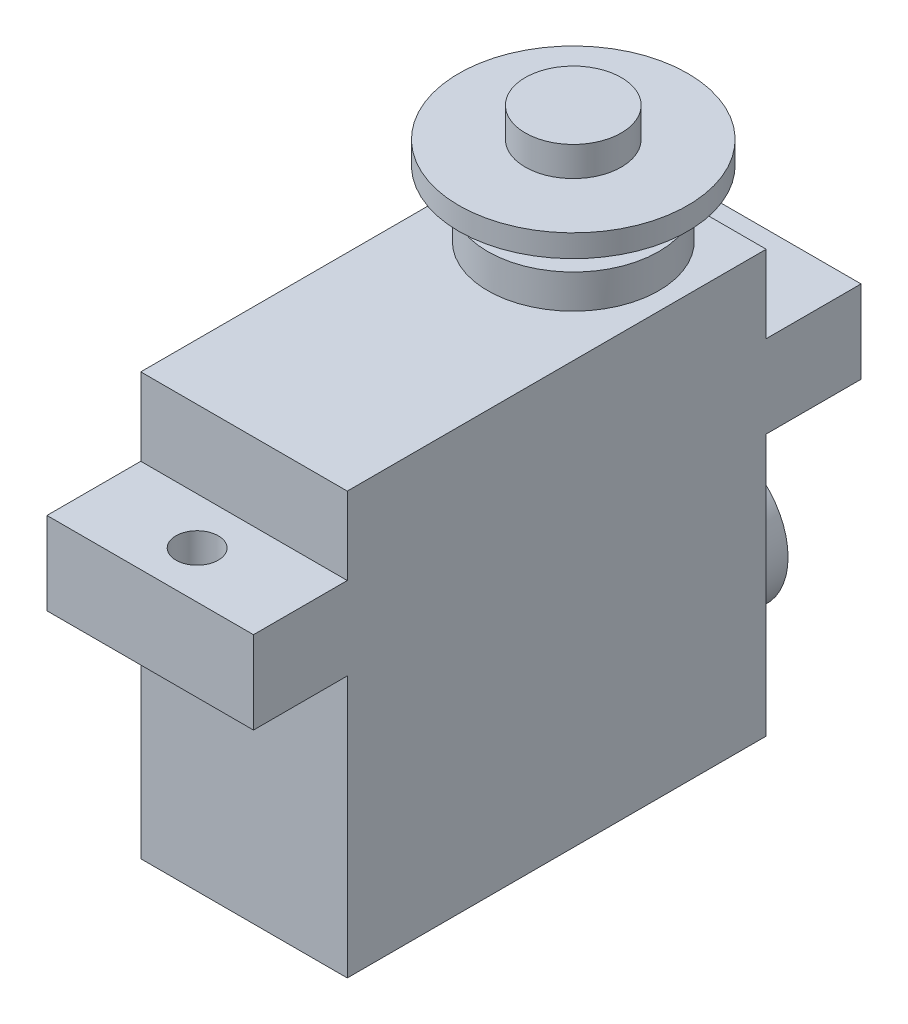
SolidWorks part; units mm, degrees
ref_plane "Front Plane" through (0, 0, 0) normal (0, 0, 1) x (1, 0, 0)
ref_plane "Top Plane" through (0, 0, 0) normal (0, 1, 0) x (1, 0, 0)
ref_plane "Right Plane" through (0, 0, 0) normal (1, 0, 0) x (0, 0, -1)
sketch "Sketch1" plane through (0, 0, 0) normal (0, 1, 0) x (1, 0, 0)
  line L1 (0, 0) -> (15.24, 0)
  line L2 (0, 0) -> (0, 30.9118)
  line L3 (0, 30.9118) -> (15.24, 30.9118)
  line L4 (15.24, 0) -> (15.24, 30.9118)
  dimension "D1" = 15.24
  dimension "D2" = 30.9118
extrude "Boss-Extrude1" add sketch "Sketch1" along normal blind 31.115
sketch "Sketch2" plane through (0, 0, 0) normal (0, 0, 1) x (1, 0, 0)
  line L0 (0, 31.115) -> (0, 0) construction
  line L1 (0, 25.4) -> (15.24, 25.4)
  line L2 (0, 25.4) -> (0, 19.304)
  line L3 (0, 19.304) -> (15.24, 19.304)
  line L4 (15.24, 25.4) -> (15.24, 19.304)
  line L5 (15.24, 31.115) -> (15.24, 0) construction
  line L6 (0, 0) -> (15.24, 0) construction
  dimension "D1" = 19.304
  dimension "D2" = 6.096
extrude "Boss-Extrude2" add sketch "Sketch2" along normal blind 6.9215 and the other way blind 37.9095
sketch "Sketch3" plane through (0, 0, -30.9118) normal (0, 0, -1) x (-1, 0, 0)
  line L0 (-15.24, 0) -> (0, 0) construction
  circle A0 centre (-7.62, 8.2804) radius 5.2705
  dimension "D1" = 10.541
  dimension "D2" = 8.2804
extrude "Boss-Extrude3" add sketch "Sketch3" along normal blind 3.9624
sketch "Sketch4" plane through (0, 31.115, 0) normal (0, 1, 0) x (1, 0, 0)
  line L0 (15.24, 30.9118) -> (0, 30.9118) construction
  circle A0 centre (7.62, 24.2951) radius 6.3119
  dimension "D1" = 12.6238
  dimension "D2" = 6.6167
extrude "Boss-Extrude4" add sketch "Sketch4" along normal blind 2.5019
sketch "Sketch5" plane through (0, 33.6169, 0) normal (0, 1, 0) x (1, 0, 0)
  circle A0 centre (7.62, 24.2951) radius 3.9942
  dimension "D1" = 7.9883
extrude "Boss-Extrude5" add sketch "Sketch5" along normal blind 2.3622
sketch "Sketch6" plane through (0, 35.9791, 0) normal (0, 1, 0) x (1, 0, 0)
  circle A0 centre (7.62, 24.2951) radius 8.4455
  dimension "D1" = 16.891
extrude "Boss-Extrude6" add sketch "Sketch6" along normal blind 1.651
sketch "Sketch7" plane through (0, 37.6301, 0) normal (0, 1, 0) x (1, 0, 0)
  circle A0 centre (7.62, 24.2951) radius 3.5433
  dimension "D1" = 7.0866
extrude "Boss-Extrude7" add sketch "Sketch7" along normal blind 2.1844
sketch "Sketch8" plane through (0, 25.4, 0) normal (0, 1, 0) x (1, 0, 0)
  circle A0 centre (7.62, -3.4608) radius 1.5621
  dimension "D1" = 3.1242
extrude "Cut-Extrude1" cut sketch "Sketch8" against normal up to next
sketch "Sketch9" plane through (0, 25.4, 0) normal (0, 1, 0) x (1, 0, 0)
  circle A0 centre (7.62, 34.4107) radius 1.5621
  dimension "D1" = 3.1242
extrude "Cut-Extrude2" cut sketch "Sketch9" against normal up to next
